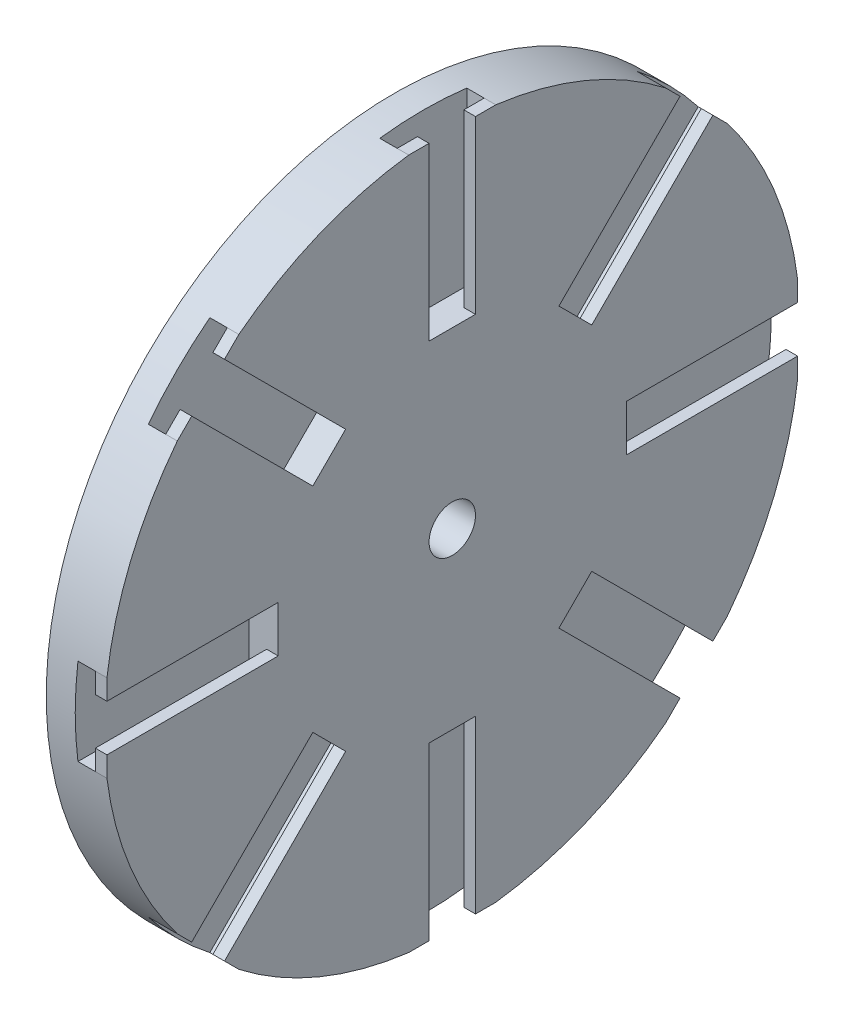
SolidWorks part; units mm, degrees
ref_plane "Front Plane" through (0, 0, 0) normal (0, 0, 1) x (1, 0, 0)
ref_plane "Top Plane" through (0, 0, 0) normal (0, 1, 0) x (1, 0, 0)
ref_plane "Right Plane" through (0, 0, 0) normal (1, 0, 0) x (0, 0, -1)
sketch "Sketch1" plane through (0, 0, 0) normal (0, 0, 1) x (1, 0, 0)
  line L0 (0, 4) -> (0, 60)
  line L1 (0, 60) -> (-10, 60)
  line L2 (-10, 60) -> (-10, 15)
  line L3 (-10, 15) -> (-25, 15)
  line L4 (-25, 15) -> (-25, 4)
  line L6 (-25, 4) -> (0, 4)
  line L7 (0, 0) -> (-22.8797, 0) construction
  dimension "D3" = 10
revolve "Revolve2" add sketch "Sketch1" angle 360 about L7
sketch "Sketch2" plane through (0, 0, 0) normal (1, 0, 0) x (0, 0, -1)
  line L0 (0, 0) -> (0, 45) construction
  line L1 (15.9099, 26.5165) -> (37.1231, 47.7297)
  line L2 (7.5, 30) -> (-7.5, 30)
  line L3 (7.5, 30) -> (7.5, 60)
  line L4 (7.5, 60) -> (-7.5, 60)
  line L5 (-7.5, 30) -> (-7.5, 60)
  line L6 (7.5, 30) -> (-7.5, 60) construction
  line L7 (7.5, 60) -> (-7.5, 30) construction
  line L8 (26.5165, 15.9099) -> (15.9099, 26.5165)
  line L9 (26.5165, 15.9099) -> (47.7297, 37.1231)
  line L10 (47.7297, 37.1231) -> (37.1231, 47.7297)
  line L11 (30, 7.5) -> (60, 7.5)
  line L12 (30, -7.5) -> (30, 7.5)
  line L13 (30, -7.5) -> (60, -7.5)
  line L14 (60, -7.5) -> (60, 7.5)
  line L15 (26.5165, -15.9099) -> (47.7297, -37.1231)
  line L16 (15.9099, -26.5165) -> (26.5165, -15.9099)
  line L17 (15.9099, -26.5165) -> (37.1231, -47.7297)
  line L18 (37.1231, -47.7297) -> (47.7297, -37.1231)
  line L19 (7.5, -30) -> (7.5, -60)
  line L20 (-7.5, -30) -> (7.5, -30)
  line L21 (-7.5, -30) -> (-7.5, -60)
  line L22 (-7.5, -60) -> (7.5, -60)
  line L23 (-15.9099, -26.5165) -> (-37.1231, -47.7297)
  line L24 (-26.5165, -15.9099) -> (-15.9099, -26.5165)
  line L25 (-26.5165, -15.9099) -> (-47.7297, -37.1231)
  line L26 (-47.7297, -37.1231) -> (-37.1231, -47.7297)
  line L27 (-30, -7.5) -> (-60, -7.5)
  line L28 (-30, 7.5) -> (-30, -7.5)
  line L29 (-30, 7.5) -> (-60, 7.5)
  line L30 (-60, 7.5) -> (-60, -7.5)
  line L31 (-26.5165, 15.9099) -> (-47.7297, 37.1231)
  line L32 (-15.9099, 26.5165) -> (-26.5165, 15.9099)
  line L33 (-15.9099, 26.5165) -> (-37.1231, 47.7297)
  line L34 (-37.1231, 47.7297) -> (-47.7297, 37.1231)
  circle A0 centre (0, 0) radius 60 construction
  dimension "D3" = 45
  dimension "D1" = 15
  dimension "D2" = 30
  dimension "D4" = 8
extrude "Cut-Extrude1" cut sketch "Sketch2" against normal blind 5
sketch "Sketch3" plane through (0, 0, 0) normal (1, 0, 0) x (0, 0, -1)
  line L0 (7.5, 60) -> (-7.5, 60) construction
  line L1 (4, 30) -> (-4, 30)
  line L2 (4, 30) -> (4, 60)
  line L3 (4, 60) -> (-4, 60)
  line L4 (-4, 30) -> (-4, 60)
  line L5 (4, 30) -> (-4, 60) construction
  line L6 (4, 60) -> (-4, 30) construction
  line L7 (-7.5, 59.5294) -> (7.5, 59.5294)
  line L8 (36.7903, 47.3969) -> (47.3969, 36.7903)
  line L9 (18.3848, 24.0416) -> (39.598, 45.2548)
  line L10 (15.9099, 26.5165) -> (36.7903, 47.3969)
  line L11 (47.3969, 36.7903) -> (26.5165, 15.9099)
  line L12 (24.0416, 18.3848) -> (45.2548, 39.598)
  line L13 (59.5294, 7.5) -> (59.5294, -7.5)
  line L14 (30, 4) -> (60, 4)
  line L15 (30, 7.5) -> (59.5294, 7.5)
  line L16 (59.5294, -7.5) -> (30, -7.5)
  line L17 (30, -4) -> (60, -4)
  line L18 (47.3969, -36.7903) -> (36.7903, -47.3969)
  line L19 (24.0416, -18.3848) -> (45.2548, -39.598)
  line L20 (26.5165, -15.9099) -> (47.3969, -36.7903)
  line L21 (36.7903, -47.3969) -> (15.9099, -26.5165)
  line L22 (18.3848, -24.0416) -> (39.598, -45.2548)
  line L23 (7.5, -59.5294) -> (-7.5, -59.5294)
  line L24 (-36.7903, 47.3969) -> (-15.9099, 26.5165)
  line L25 (-15.9099, 26.5165) -> (-26.5165, 15.9099)
  line L26 (-26.5165, 15.9099) -> (-47.3969, 36.7903)
  line L27 (-59.5294, 7.5) -> (-30, 7.5)
  line L28 (-30, 7.5) -> (-30, -7.5)
  line L29 (-30, -7.5) -> (-59.5294, -7.5)
  line L30 (-47.3969, -36.7903) -> (-26.5165, -15.9099)
  line L31 (-26.5165, -15.9099) -> (-15.9099, -26.5165)
  line L32 (-15.9099, -26.5165) -> (-36.7903, -47.3969)
  line L33 (-7.5, -59.5294) -> (-7.5, -30)
  line L34 (-7.5, -30) -> (7.5, -30)
  line L35 (7.5, -30) -> (7.5, -59.5294)
  line L36 (36.7903, -47.3969) -> (15.9099, -26.5165)
  line L37 (15.9099, -26.5165) -> (26.5165, -15.9099)
  line L38 (26.5165, -15.9099) -> (47.3969, -36.7903)
  line L39 (59.5294, -7.5) -> (30, -7.5)
  line L40 (30, -7.5) -> (30, 7.5)
  line L41 (30, 7.5) -> (59.5294, 7.5)
  line L42 (47.3969, 36.7903) -> (26.5165, 15.9099)
  line L43 (26.5165, 15.9099) -> (15.9099, 26.5165)
  line L44 (15.9099, 26.5165) -> (36.7903, 47.3969)
  line L45 (7.5, 59.5294) -> (7.5, 30)
  line L46 (7.5, 30) -> (-7.5, 30)
  line L47 (-7.5, 30) -> (-7.5, 59.5294)
  line L48 (-36.7903, 47.3969) -> (-15.9099, 26.5165)
  line L49 (-15.9099, 26.5165) -> (-26.5165, 15.9099)
  line L50 (-26.5165, 15.9099) -> (-47.3969, 36.7903)
  line L51 (-59.5294, 7.5) -> (-30, 7.5)
  line L52 (-30, 7.5) -> (-30, -7.5)
  line L53 (-30, -7.5) -> (-59.5294, -7.5)
  line L54 (-47.3969, -36.7903) -> (-26.5165, -15.9099)
  line L55 (-26.5165, -15.9099) -> (-15.9099, -26.5165)
  line L56 (-15.9099, -26.5165) -> (-36.7903, -47.3969)
  line L57 (-7.5, -59.5294) -> (-7.5, -30)
  line L58 (-7.5, -30) -> (7.5, -30)
  line L59 (7.5, -30) -> (7.5, -59.5294)
  line L60 (36.7903, -47.3969) -> (15.9099, -26.5165)
  line L61 (15.9099, -26.5165) -> (26.5165, -15.9099)
  line L62 (26.5165, -15.9099) -> (47.3969, -36.7903)
  line L63 (59.5294, -7.5) -> (30, -7.5)
  line L64 (30, -7.5) -> (30, 7.5)
  line L65 (30, 7.5) -> (59.5294, 7.5)
  line L66 (47.3969, 36.7903) -> (26.5165, 15.9099)
  line L67 (26.5165, 15.9099) -> (15.9099, 26.5165)
  line L68 (15.9099, 26.5165) -> (36.7903, 47.3969)
  line L69 (7.5, 59.5294) -> (7.5, 30)
  line L70 (7.5, 30) -> (-7.5, 30)
  line L71 (-7.5, 30) -> (-7.5, 59.5294)
  line L72 (4, -30) -> (4, -60)
  line L73 (7.5, -30) -> (7.5, -59.5294)
  line L74 (-7.5, -59.5294) -> (-7.5, -30)
  line L75 (-4, -30) -> (-4, -60)
  line L76 (-36.7903, -47.3969) -> (-47.3969, -36.7903)
  line L77 (-18.3848, -24.0416) -> (-39.598, -45.2548)
  line L78 (-15.9099, -26.5165) -> (-36.7903, -47.3969)
  line L79 (-47.3969, -36.7903) -> (-26.5165, -15.9099)
  line L80 (-24.0416, -18.3848) -> (-45.2548, -39.598)
  line L81 (-59.5294, -7.5) -> (-59.5294, 7.5)
  line L82 (-30, -4) -> (-60, -4)
  line L83 (-30, -7.5) -> (-59.5294, -7.5)
  line L84 (-59.5294, 7.5) -> (-30, 7.5)
  line L85 (-30, 4) -> (-60, 4)
  line L86 (-47.3969, 36.7903) -> (-36.7903, 47.3969)
  line L87 (-24.0416, 18.3848) -> (-45.2548, 39.598)
  line L88 (-26.5165, 15.9099) -> (-47.3969, 36.7903)
  line L89 (-36.7903, 47.3969) -> (-15.9099, 26.5165)
  line L90 (-18.3848, 24.0416) -> (-39.598, 45.2548)
  arc A8 (-47.3969, 36.7903) -> (-59.5294, 7.5) centre (0, 0) ccw
  arc A9 (-59.5294, -7.5) -> (-47.3969, -36.7903) centre (0, 0) ccw
  arc A10 (-36.7903, -47.3969) -> (-7.5, -59.5294) centre (0, 0) ccw
  arc A11 (7.5, -59.5294) -> (36.7903, -47.3969) centre (0, 0) ccw
  arc A12 (47.3969, -36.7903) -> (59.5294, -7.5) centre (0, 0) ccw
  arc A13 (59.5294, 7.5) -> (47.3969, 36.7903) centre (0, 0) ccw
  arc A14 (36.7903, 47.3969) -> (7.5, 59.5294) centre (0, 0) ccw
  arc A15 (-7.5, 59.5294) -> (-36.7903, 47.3969) centre (0, 0) ccw
  arc A16 (-47.3969, 36.7903) -> (-59.5294, 7.5) centre (0, 0) ccw
  arc A17 (-59.5294, -7.5) -> (-47.3969, -36.7903) centre (0, 0) ccw
  arc A18 (-36.7903, -47.3969) -> (-7.5, -59.5294) centre (0, 0) ccw
  arc A19 (7.5, -59.5294) -> (36.7903, -47.3969) centre (0, 0) ccw
  arc A20 (47.3969, -36.7903) -> (59.5294, -7.5) centre (0, 0) ccw
  arc A21 (59.5294, 7.5) -> (47.3969, 36.7903) centre (0, 0) ccw
  arc A22 (36.7903, 47.3969) -> (7.5, 59.5294) centre (0, 0) ccw
  arc A23 (-7.5, 59.5294) -> (-36.7903, 47.3969) centre (0, 0) ccw
  point P6 (0, 45)
  line M33 (-36.7903, 47.3969) -> (-15.9099, 26.5165)
  line M34 (-15.9099, 26.5165) -> (-26.5165, 15.9099)
  line M35 (-26.5165, 15.9099) -> (-47.3969, 36.7903)
  line M37 (-59.5294, 7.5) -> (-30, 7.5)
  line M38 (-30, 7.5) -> (-30, -7.5)
  line M39 (-30, -7.5) -> (-59.5294, -7.5)
  line M41 (-47.3969, -36.7903) -> (-26.5165, -15.9099)
  line M42 (-26.5165, -15.9099) -> (-15.9099, -26.5165)
  line M43 (-15.9099, -26.5165) -> (-36.7903, -47.3969)
  line M45 (-7.5, -59.5294) -> (-7.5, -30)
  line M46 (-7.5, -30) -> (7.5, -30)
  line M47 (7.5, -30) -> (7.5, -59.5294)
  line M49 (36.7903, -47.3969) -> (15.9099, -26.5165)
  line M50 (15.9099, -26.5165) -> (26.5165, -15.9099)
  line M51 (26.5165, -15.9099) -> (47.3969, -36.7903)
  line M53 (59.5294, -7.5) -> (30, -7.5)
  line M54 (30, -7.5) -> (30, 7.5)
  line M55 (30, 7.5) -> (59.5294, 7.5)
  line M57 (47.3969, 36.7903) -> (26.5165, 15.9099)
  line M58 (26.5165, 15.9099) -> (15.9099, 26.5165)
  line M59 (15.9099, 26.5165) -> (36.7903, 47.3969)
  line M61 (7.5, 59.5294) -> (7.5, 30)
  line M62 (7.5, 30) -> (-7.5, 30)
  line M63 (-7.5, 30) -> (-7.5, 59.5294)
  dimension "D2" = 8
  dimension "D1" = 0
  dimension "D3" = 8
extrude "Boss-Extrude1" add sketch "Sketch3" against normal blind 2 contours L90 L86 M34 M33 | L49 L87 L86 M35 | L85 L81 M38 M37 | L52 L82 L81 M39 | L80 L76 M42 M41 | L55 L77 L76 M43 | L75 L23 M46 M45 | L58 L72 L23 M47 | L22 L18 M50 M49 | L19 L18 M50 M51 | L17 L13 M54 M53 | L14 L13 M54 M55 | L12 L8 M58 M57 | L9 L8 M58 M59 | L7 L2 M62 M61 | L7 L4 M63 M62
